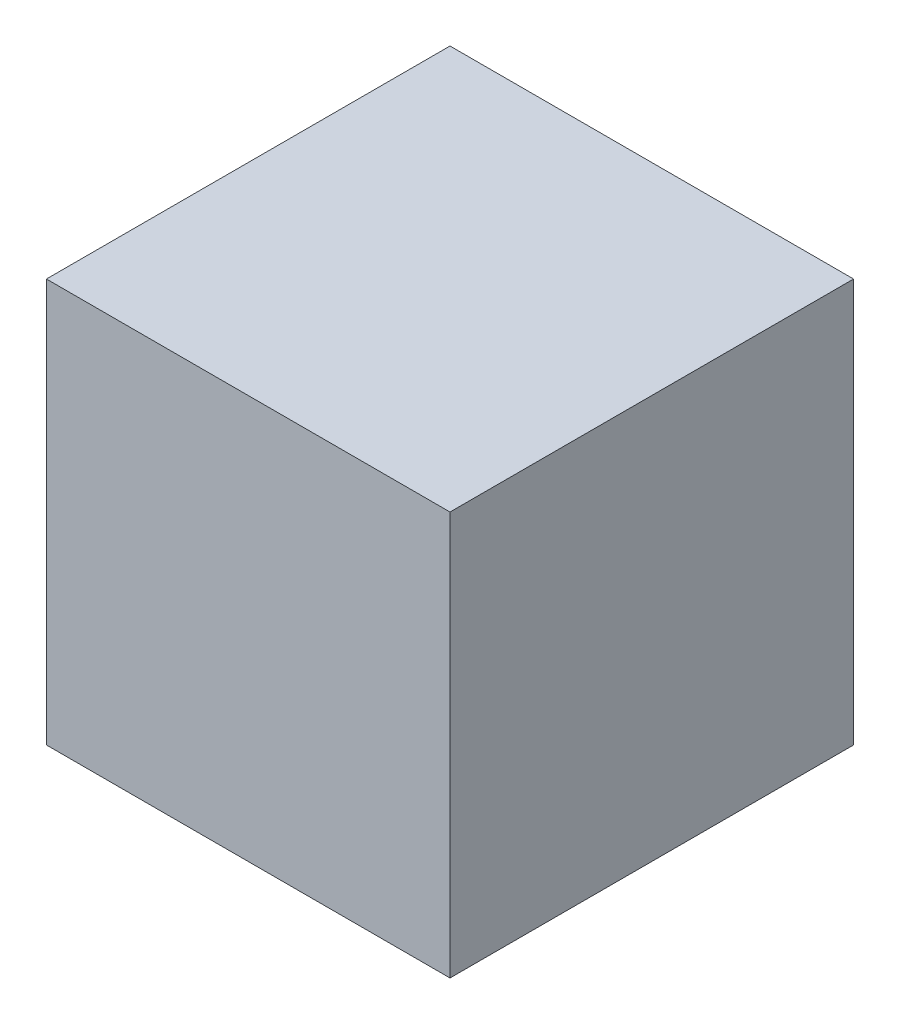
SolidWorks part; units mm, degrees
ref_plane "前视基准面" through (0, 0, 0) normal (0, 0, 1) x (1, 0, 0)
ref_plane "上视基准面" through (0, 0, 0) normal (0, 1, 0) x (1, 0, 0)
ref_plane "右视基准面" through (0, 0, 0) normal (1, 0, 0) x (0, 0, -1)
sketch "草图1" plane through (0, 0, 0) normal (0, 1, 0) x (1, 0, 0)
  line L1 (-20, -20) -> (20, -20)
  line L2 (-20, -20) -> (-20, 20)
  line L3 (-20, 20) -> (20, 20)
  line L4 (20, -20) -> (20, 20)
  line L5 (-20, -20) -> (20, 20) construction
  line L6 (-20, 20) -> (20, -20) construction
  point P0 (0, 0)
extrude "凸台-拉伸1" add sketch "草图1" along normal blind 40
